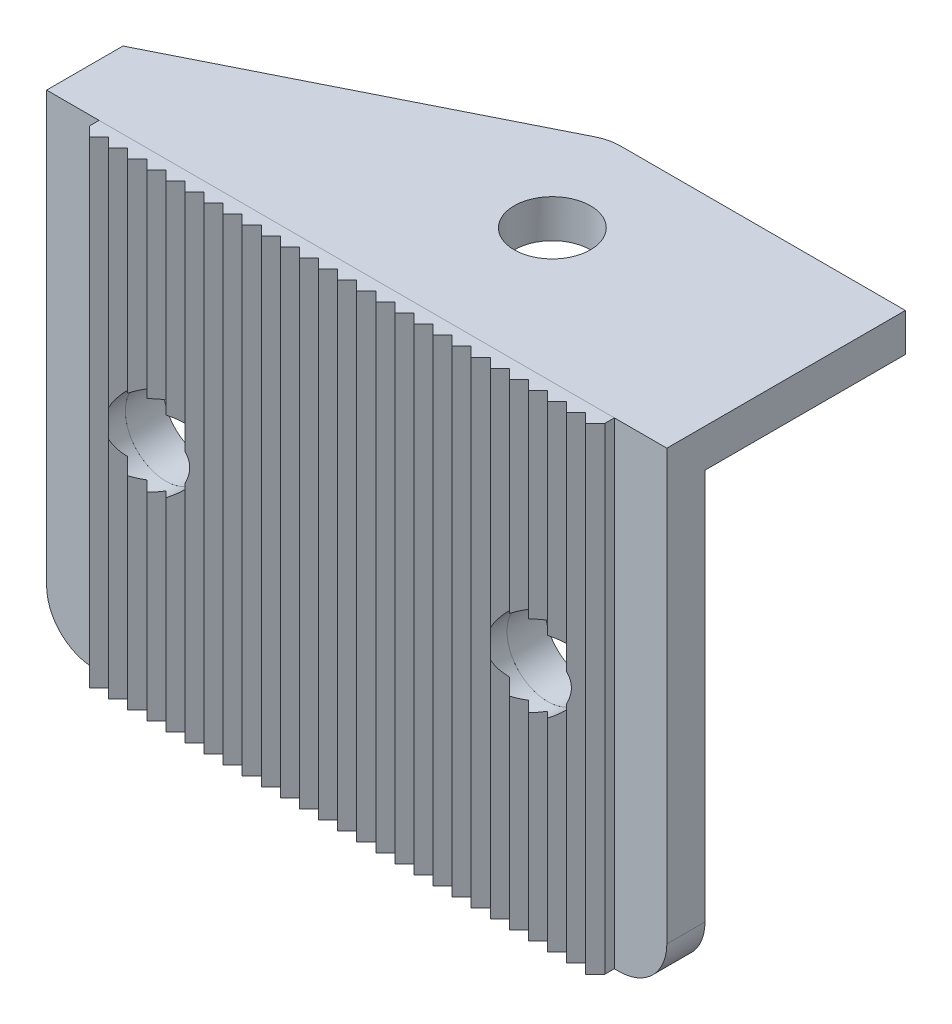
SolidWorks part; units mm, degrees
material "Alu 5754 (AG3)"
ref_plane "Face" through (0, 0, 0) normal (0, 0, 1) x (1, 0, 0)
ref_plane "Dessus" through (0, 0, 0) normal (0, 1, 0) x (1, 0, 0)
ref_plane "Droite" through (0, 0, 0) normal (1, 0, 0) x (0, 0, -1)
sketch "Esquisse1" plane through (0, 0, 0) normal (0, 0, 1) x (1, 0, 0)
  line L1 (-32.5, 25) -> (32.5, 25)
  line L2 (-32.5, 25) -> (-32.5, -20)
  line L3 (-27.5, -25) -> (27.5, -25)
  line L4 (32.5, 25) -> (32.5, -20)
  line L5 (-32.5, 25) -> (32.5, -25) construction
  line L6 (-32.5, -25) -> (32.5, 25) construction
  arc A0 (-32.5, -20) -> (-27.5, -25) centre (-27.5, -20) ccw
  arc A1 (27.5, -25) -> (32.5, -20) centre (27.5, -20) ccw
  point P0 (0, 0)
  dimension "D3" = 5
  dimension "D1" = 65
  dimension "D2" = 50
extrude "Boss.-Extru.1" add sketch "Esquisse1" along normal blind 4
sketch "Esquisse3" plane through (0, 25, 0) normal (0, 1, 0) x (1, 0, 0)
  line L0 (-32.5, 0) -> (-32.5, 4)
  line L1 (-32.5, 4) -> (1.5, 21)
  line L2 (1.5, 21) -> (32.5, 21)
  line L3 (32.5, 21) -> (32.5, 0)
  line L4 (32.5, 0) -> (-32.5, 0)
  dimension "D1" = 21
  dimension "D2" = 4
  dimension "D3" = 31
extrude "Boss.-Extru.2" add sketch "Esquisse3" against normal blind 4
fillet "Congé1" radius 5 1 edges at (1.5, 23, -21)
sketch "Esquisse4" plane through (0, 0, 4) normal (0, 0, 1) x (1, 0, 0)
  line L0 (32.5, 25) -> (-32.5, 25) construction
  line L1 (0, 0) -> (0, 25) construction
  circle A0 centre (-20, 0) radius 4.25
  circle A1 centre (20, 0) radius 4.25
  dimension "D3" = 8.5
  dimension "D1" = 25
  dimension "D2" = 20
extrude "Enlèv. mat.-Extru.1" cut sketch "Esquisse4" against normal up to surface (4 mm away) up to face at (-5.4167, -8.3452, 0)
sketch "Esquisse5" plane through (0, 25, 0) normal (0, 1, 0) x (1, 0, 0)
  line L0 (32.5, -4) -> (32.5, 21) construction
  line L1 (32.5, -4) -> (-32.5, -4) construction
  circle A0 centre (6.5, 10) radius 4
  dimension "D1" = 8
  dimension "D3" = 14
  dimension "D2" = 26
extrude "Enlèv. mat.-Extru.2" cut sketch "Esquisse5" against normal up to surface (4 mm away) up to face at (-4.901, 21, -9.6837)
sketch "Esquisse6" plane through (-7.5, -25, 0) normal (0, 1, 0) x (0, 0, 1)
  line L0 (4, -19.5) -> (5, -19.5)
  line L1 (5, -19.5) -> (6, -18.5)
  line L2 (6, -18.5) -> (5, -17.5)
  line L3 (6, -16.5) -> (5, -15.5)
  line L4 (5, -17.5) -> (6, -16.5)
  line L5 (6, -14.5) -> (5, -13.5)
  line L6 (5, -15.5) -> (6, -14.5)
  line L7 (6, -12.5) -> (5, -11.5)
  line L8 (5, -13.5) -> (6, -12.5)
  line L9 (6, -10.5) -> (5, -9.5)
  line L10 (5, -11.5) -> (6, -10.5)
  line L11 (6, -8.5) -> (5, -7.5)
  line L12 (5, -9.5) -> (6, -8.5)
  line L13 (6, -6.5) -> (5, -5.5)
  line L14 (5, -7.5) -> (6, -6.5)
  line L15 (6, -4.5) -> (5, -3.5)
  line L16 (5, -5.5) -> (6, -4.5)
  line L17 (6, -2.5) -> (5, -1.5)
  line L18 (5, -3.5) -> (6, -2.5)
  line L19 (6, -0.5) -> (5, 0.5)
  line L20 (5, -1.5) -> (6, -0.5)
  line L21 (6, 1.5) -> (5, 2.5)
  line L22 (5, 0.5) -> (6, 1.5)
  line L23 (6, 3.5) -> (5, 4.5)
  line L24 (5, 2.5) -> (6, 3.5)
  line L25 (6, 5.5) -> (5, 6.5)
  line L26 (5, 4.5) -> (6, 5.5)
  line L27 (6, 7.5) -> (5, 8.5)
  line L28 (5, 6.5) -> (6, 7.5)
  line L29 (6, 9.5) -> (5, 10.5)
  line L30 (5, 8.5) -> (6, 9.5)
  line L31 (6, 11.5) -> (5, 12.5)
  line L32 (5, 10.5) -> (6, 11.5)
  line L33 (6, 13.5) -> (5, 14.5)
  line L34 (5, 12.5) -> (6, 13.5)
  line L35 (6, 15.5) -> (5, 16.5)
  line L36 (5, 14.5) -> (6, 15.5)
  line L37 (6, 17.5) -> (5, 18.5)
  line L38 (5, 16.5) -> (6, 17.5)
  line L39 (6, 19.5) -> (5, 20.5)
  line L40 (5, 18.5) -> (6, 19.5)
  line L41 (6, 21.5) -> (5, 22.5)
  line L42 (5, 20.5) -> (6, 21.5)
  line L43 (6, 23.5) -> (5, 24.5)
  line L44 (5, 22.5) -> (6, 23.5)
  line L45 (6, 25.5) -> (5, 26.5)
  line L46 (5, 24.5) -> (6, 25.5)
  line L47 (6, 27.5) -> (5, 28.5)
  line L48 (5, 26.5) -> (6, 27.5)
  line L49 (6, 29.5) -> (5, 30.5)
  line L50 (5, 28.5) -> (6, 29.5)
  line L51 (6, 31.5) -> (5, 32.5)
  line L52 (5, 30.5) -> (6, 31.5)
  line L53 (6, 33.5) -> (5, 34.5)
  line L54 (5, 32.5) -> (6, 33.5)
  line L55 (5, 34.5) -> (4, 34.5)
  line L56 (4, -20) -> (4, 35) construction
  line L57 (4, 34.5) -> (4, -19.5)
  line L58 (4, -20) -> (0, -20) construction
  dimension "D1" = 45
  dimension "D2" = 1
  dimension "D3" = 2
  dimension "D5" = 0.5
  dimension "D4" = 27
extrude "Boss.-Extru.3" add sketch "Esquisse6" along normal up to surface (50 mm away) separate body up to face at (6.5, 25, -6)
sketch "Esquisse7" plane through (0, 0, 4) normal (0, 0, -1) x (-1, 0, 0)
  circle A0 centre (-20, 0) radius 4.25 construction
  circle A1 centre (20, 0) radius 4.25 construction
  circle A2 centre (-20, 0) radius 4.25
  circle A3 centre (20, 0) radius 4.25
extrude "Enlèv. mat.-Extru.3" cut sketch "Esquisse7" against normal through all
